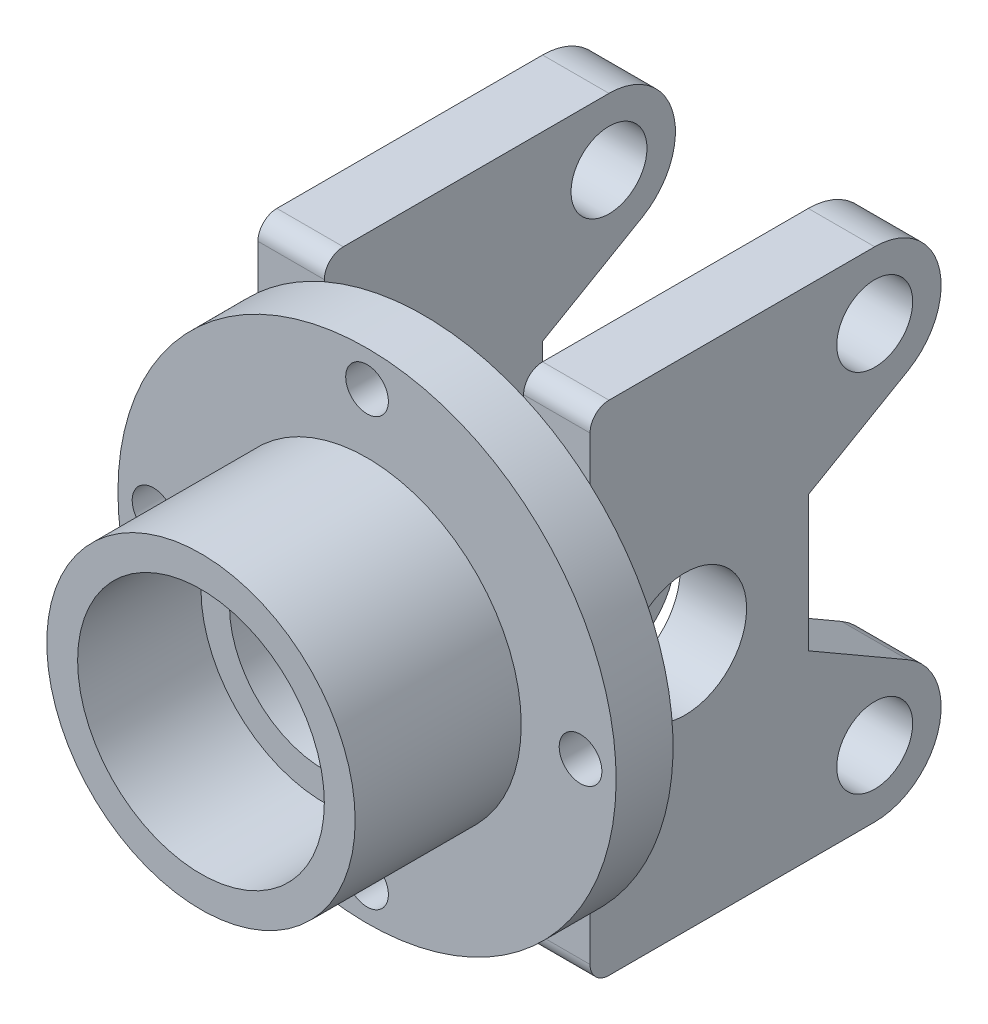
SolidWorks part; units mm, degrees
ref_plane "前视基准面" through (0, 0, 0) normal (0, 0, 1) x (1, 0, 0)
ref_plane "上视基准面" through (0, 0, 0) normal (0, 1, 0) x (1, 0, 0)
ref_plane "右视基准面" through (0, 0, 0) normal (1, 0, 0) x (0, 0, -1)
other "Configuration Table"
sketch "草图1" plane through (0, 0, 0) normal (0, 0, 1) x (1, 0, 0)
  circle A0 centre (0, 0) radius 32.5
  dimension "D1" = 65
extrude "凸台-拉伸1" add sketch "草图1" against normal blind 35
sketch "草图2" plane through (0, 0, -35) normal (0, 0, -1) x (-1, 0, 0)
  circle A0 centre (0, 0) radius 52.5
  dimension "D1" = 105
extrude "凸台-拉伸2" add sketch "草图2" along normal blind 12
sketch "草图4" plane through (0, 0, 0) normal (1, 0, 0) x (0, 0, -1)
  line L0 (0, 0) -> (164.0077, 0) construction
  line L1 (0, 32.5) -> (0, -32.5) construction
  line L2 (51, 52.5) -> (107, 52.5)
  line L3 (114, 26.3756) -> (93, 14.2513)
  line L4 (93, 14.2513) -> (93, -14.2513)
  line L5 (35, 52.5) -> (35, -52.5) construction
  line L6 (47, 48.5) -> (47, -48.5)
  line L7 (47, -52.5) -> (47, 52.5) construction
  line L8 (114, -26.3756) -> (93, -14.2513)
  line L9 (51, -52.5) -> (107, -52.5)
  arc A0 (114, 26.3756) -> (107, 52.5) centre (107, 38.5) ccw
  arc A1 (51, 52.5) -> (47, 48.5) centre (51, 48.5) ccw
  arc A2 (51, -52.5) -> (47, -48.5) centre (51, -48.5) cw
  arc A3 (114, -26.3756) -> (107, -52.5) centre (107, -38.5) cw
  point P16 (47, 52.5)
  point P26 (47, 0)
  point P27 (93, 0)
  dimension "D1" = 30
  dimension "D2" = 28
  dimension "D4" = 4
  dimension "D3" = 58
  dimension "D5" = 72
extrude "凸台-拉伸3" add sketch "草图4" along normal mid plane 70
sketch "草图6" plane through (0, 0, 0) normal (1, 0, 0) x (0, 0, -1)
  line L8 (107, 52.5) -> (51, 52.5)
  line L9 (47, 48.5) -> (47, 39.1312)
  line L10 (47, 39.1312) -> (47, -39.1312)
  line L11 (47, -39.1312) -> (47, -48.5)
  line L12 (51, -52.5) -> (107, -52.5)
  line L13 (114, -26.3756) -> (93, -14.2513)
  line L14 (93, -14.2513) -> (93, 14.2513)
  line L15 (93, 14.2513) -> (114, 26.3756)
  line L16 (107, 52.5) -> (51, 52.5)
  line L17 (47, 48.5) -> (47, 39.1312)
  line L18 (47, 39.1312) -> (47, -39.1312)
  line L19 (47, -39.1312) -> (47, -48.5)
  line L20 (51, -52.5) -> (107, -52.5)
  line L21 (114, -26.3756) -> (93, -14.2513)
  line L22 (93, -14.2513) -> (93, 14.2513)
  line L23 (93, 14.2513) -> (114, 26.3756)
  arc A4 (114, 26.3756) -> (107, 52.5) centre (107, 38.5) ccw
  arc A5 (51, 52.5) -> (47, 48.5) centre (51, 48.5) ccw
  arc A6 (47, -48.5) -> (51, -52.5) centre (51, -48.5) ccw
  arc A7 (107, -52.5) -> (114, -26.3756) centre (107, -38.5) ccw
  arc A8 (114, 26.3756) -> (107, 52.5) centre (107, 38.5) ccw
  arc A9 (51, 52.5) -> (47, 48.5) centre (51, 48.5) ccw
  arc A10 (47, -48.5) -> (51, -52.5) centre (51, -48.5) ccw
  arc A11 (107, -52.5) -> (114, -26.3756) centre (107, -38.5) ccw
  dimension "D1" = 0
extrude "切除-拉伸2" cut sketch "草图6" against normal mid plane 42
sketch "草图7" plane through (35, 0, 0) normal (1, 0, 0) x (0, 0, -1)
  line L0 (0, 0) -> (164.0077, 0) construction
  line L1 (47, 48.5) -> (47, -48.5) construction
  circle A0 centre (107, 38.5) radius 8
  circle A1 centre (107, -38.5) radius 8
  circle A2 centre (67, 0) radius 13
  dimension "D1" = 20
  dimension "D2" = 26
  dimension "D3" = 16
  dimension "D4" = 16
extrude "切除-拉伸3" cut sketch "草图7" against normal through all
sketch "草图8" plane through (0, 0, -47) normal (0, 0, -1) x (-1, 0, 0)
  circle A0 centre (0, 0) radius 45 construction
  circle A1 centre (0, 45) radius 4.5
  dimension "D1" = 90
  dimension "D2" = 9
extrude "切除-拉伸4" cut sketch "草图8" against normal through all
pattern_circular "阵列(圆周)1" count 4 over 360 about axis through (0, 0, 0) along (0, 0, 1) of "切除-拉伸4"
sketch "草图9" plane through (0, 0, -47) normal (0, 0, -1) x (-1, 0, 0)
  line L0 (0, 14.2513) -> (0, -14.2513) construction
  circle A1 centre (0, 0) radius 20
  dimension "D1" = 40
extrude "切除-拉伸5" cut sketch "草图9" against normal blind 21
sketch "草图10" plane through (0, 0, -26) normal (0, 0, -1) x (-1, 0, 0)
  circle A0 centre (0, 0) radius 26
  dimension "D1" = 52
extrude "切除-拉伸6" cut sketch "草图10" against normal through all
